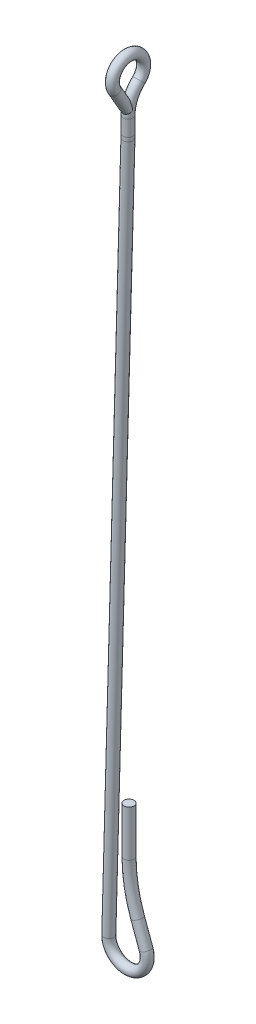
SolidWorks part; units mm, degrees
material "Nylon 6/10"
ref_plane "Front Plane" through (0, 0, 0) normal (0, 0, 1) x (1, 0, 0)
ref_plane "Top Plane" through (0, 0, 0) normal (0, 1, 0) x (1, 0, 0)
ref_plane "Right Plane" through (0, 0, 0) normal (1, 0, 0) x (0, 0, -1)
sketch "Sketch1" plane through (0, 0, 0) normal (0, 0, 1) x (1, 0, 0)
  line L0 (-6.8554, 28.7625) -> (-0.019, 278.7056)
  line L1 (0, 280.0946) -> (0, 285.75)
  line L2 (6.4444, 30.9206) -> (3.4281, 39.2078)
  line L3 (0.3645, 56.5824) -> (0.3645, 73.025)
  arc A0 (-6.8554, 28.7625) -> (6.4444, 30.9206) centre (0, 28.575) ccw
  circle A1 centre (0, 28.575) radius 5.08 construction
  arc A2 (-0.019, 278.7056) -> (0, 280.0946) centre (-50.8, 280.0946) ccw
  arc A3 (3.4281, 39.2078) -> (0.3645, 56.5824) centre (51.1645, 56.5824) cw
  point P11 (0, 279.4)
  point P18 (0.3645, 47.625)
  dimension "D1" = 1.778
  dimension "D4" = 50.8
  dimension "D8" = 50.8
  dimension "D2" = 6.35
  dimension "D3" = 19.05
  dimension "D5" = 25.4
  dimension "D6" = 160
  dimension "D7" = 44.45
ref_plane "Plane1" through (0, 285.75, 0) normal (0, 1, 0) x (1, 0, 0)
sketch "Sketch2" plane through (0, 285.75, 0) normal (0, 1, 0) x (1, 0, 0)
  circle A0 centre (0, 0) radius 1.778
  dimension "D1" = 3.556
sweep "Sweep1" add profiles "Sketch2" path "Sketch1"
sketch "Sketch3" plane through (0, 0, 0) normal (1, 0, 0) x (0, 0, -1)
  line L0 (0, 298.704) -> (0, 307.7961) construction
  line L1 (0, 298.704) -> (5.588, 298.704) construction
  line L2 (0, 280.0946) -> (0, 285.75) construction
  line L3 (1.778, 285.75) -> (-1.778, 285.75) construction
  line L4 (1.778, 285.75) -> (-1.778, 285.75) construction
  line L5 (0, 285.75) -> (0, 296.2846) construction
  line L6 (-4.8393, 295.91) -> (-0.254, 287.9679)
  line L7 (0, 298.704) -> (0, 307.7961) construction
  arc A0 (3.8346, 294.6393) -> (-4.8393, 295.91) centre (0, 298.704) ccw
  arc A1 (3.8346, 294.6393) -> (0, 285.75) centre (12.2209, 285.75) ccw
  dimension "D1" = 5.588
  dimension "D2" = 0.254
  dimension "D3" = 30
sketch "Sketch4" plane through (0, 285.75, 0) normal (0, 1, 0) x (1, 0, 0)
  circle A1 centre (0, 0) radius 1.778
  circle A2 centre (0, 0) radius 1.778
  dimension "D1" = 0
sweep "Sweep2" add profiles "Sketch4" path "Sketch3"
